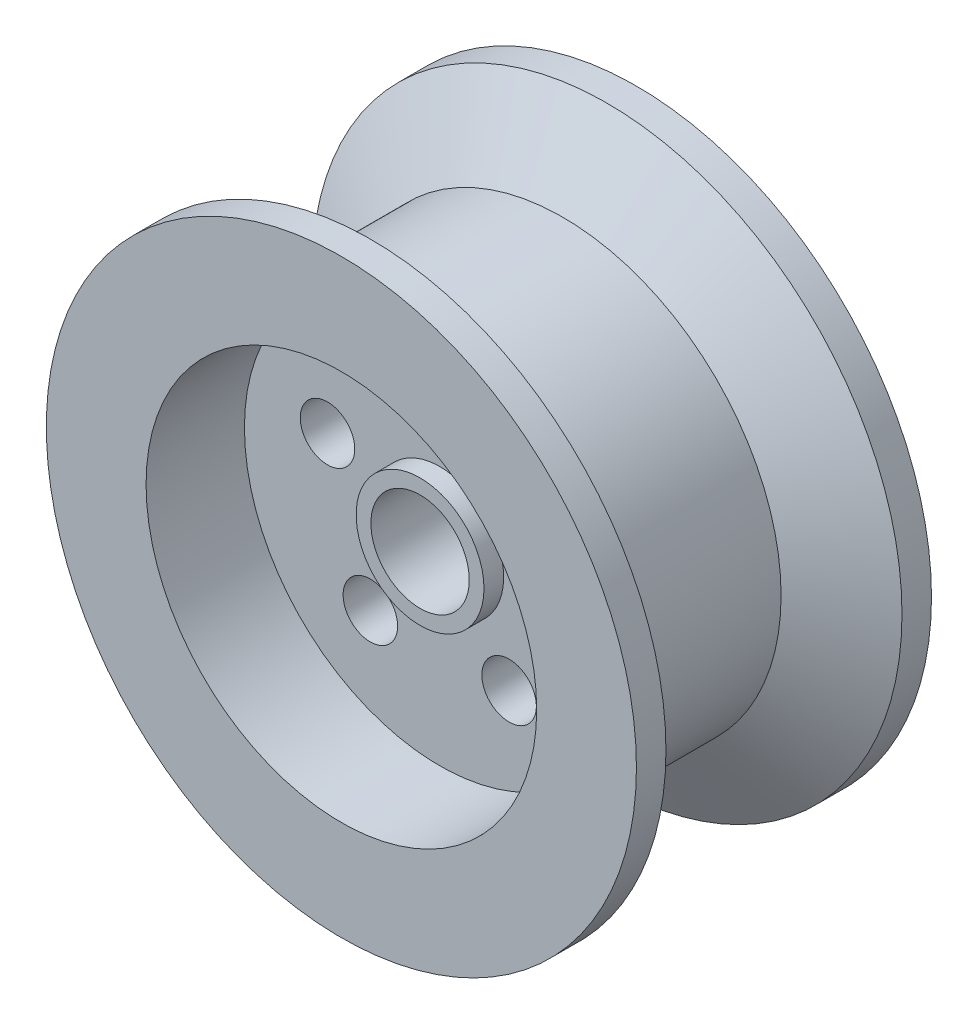
SolidWorks part; units mm, degrees
ref_plane "Front Plane" through (0, 0, 0) normal (0, 0, 1) x (1, 0, 0)
ref_plane "Top Plane" through (0, 0, 0) normal (0, 1, 0) x (1, 0, 0)
ref_plane "Right Plane" through (0, 0, 0) normal (1, 0, 0) x (0, 0, -1)
sketch "Sketch1" plane through (0, 0, 0) normal (0, 0, 1) x (1, 0, 0)
  circle A0 centre (0, 0) radius 30
  circle A1 centre (0, 0) radius 5
  dimension "D1" = 60
  dimension "D2" = 10
extrude "Boss-Extrude3" add sketch "Sketch1" along normal blind 30
sketch "Sketch2" plane through (0, 0, 30) normal (0, 0, 1) x (1, 0, 0)
  circle A0 centre (0, 0) radius 19.8581
extrude "Cut-Extrude1" cut sketch "Sketch2" against normal blind 10
mirror "Mirror1" about plane through (0, 0, 0) normal (0, 0, 1) of "Cut-Extrude1"
sketch "Sketch3" plane through (0, 0, 20) normal (0, 0, 1) x (1, 0, 0)
  circle A0 centre (0, 12) radius 2.7714
  circle A1 centre (11.4127, 3.7082) radius 2.7714
  circle A2 centre (7.0534, -9.7082) radius 2.7714
  circle A3 centre (-7.0534, -9.7082) radius 2.7714
  circle A4 centre (-11.4127, 3.7082) radius 2.7714
  point P13 (0, 0)
  dimension "D1" = 12
  dimension "D2" = 5
extrude "Cut-Extrude2" cut sketch "Sketch3" against normal through all
sketch "Sketch4" plane through (0, 0, 20) normal (0, 0, 1) x (1, 0, 0)
  circle A0 centre (0, 0) radius 6.5
  circle A1 centre (0, 0) radius 5
  dimension "D1" = 13
  dimension "D2" = 10
extrude "Boss-Extrude4" add sketch "Sketch4" along normal blind 2 and the other way blind 7
sketch "Sketch5" plane through (0, 0, 0) normal (0, 1, 0) x (1, 0, 0)
  line L0 (0, 0) -> (0, 8.5676) construction
  line L1 (30, -3) -> (22.2058, -7.5)
  line L2 (30, -30) -> (30, 0) construction
  line L3 (22.2058, -7.5) -> (22.2058, -22.5)
  line L4 (22.2058, -22.5) -> (30, -27)
  line L5 (30, -3) -> (30, -27)
  dimension "D1" = 3
  dimension "D2" = 3
  dimension "D3" = 60
  dimension "D4" = 60
  dimension "D5" = 15
revolve "Cut-Revolve1" cut sketch "Sketch5" angle 360 about L0
